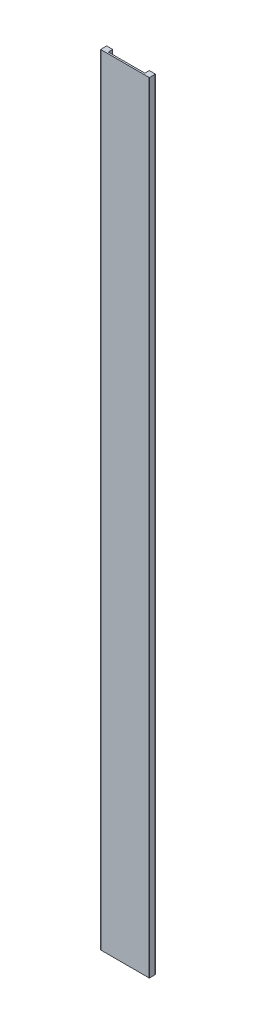
SolidWorks part; units mm, degrees
material "6061-T6 (SS)"
ref_plane "Front Plane" through (0, 0, 0) normal (0, 0, 1) x (1, 0, 0)
ref_plane "Top Plane" through (0, 0, 0) normal (0, 1, 0) x (1, 0, 0)
ref_plane "Right Plane" through (0, 0, 0) normal (1, 0, 0) x (0, 0, -1)
sketch "Sketch2" plane through (0, 0, 0) normal (0, 1, 0) x (1, 0, 0)
  line L0 (-38.1, 0) -> (38.1, 0)
  line L1 (38.1, 0) -> (38.1, 9.525)
  line L2 (38.1, 9.525) -> (28.575, 9.525)
  line L3 (28.575, 9.525) -> (28.575, 2.54)
  line L4 (28.575, 2.54) -> (-28.575, 2.54)
  line L5 (0, 0) -> (0, 20.137) construction
  line L6 (-28.575, 9.525) -> (-28.575, 2.54)
  line L7 (-38.1, 9.525) -> (-28.575, 9.525)
  line L8 (-38.1, 0) -> (-38.1, 9.525)
  point P9 (0, 2.54)
  point P12 (-38.1, 4.7625)
  point P13 (38.1, 4.7625)
  point P14 (28.575, 6.0325)
  dimension "D1" = 9.525
  dimension "D2" = 76.2
  dimension "D3" = 9.525
  dimension "D4" = 2.54
extrude "Boss-Extrude1" add sketch "Sketch2" along normal blind 1219.2
fillet "Fillet1" radius 0.381 8 edges at (-38.1, 609.6, 0) (28.575, 609.6, -2.54) (38.1, 609.6, 0) (38.1, 609.6, -9.525) (28.575, 609.6, -9.525) (-38.1, 609.6, -9.525) (-28.575, 609.6, -9.525) (-28.575, 609.6, -2.54)
